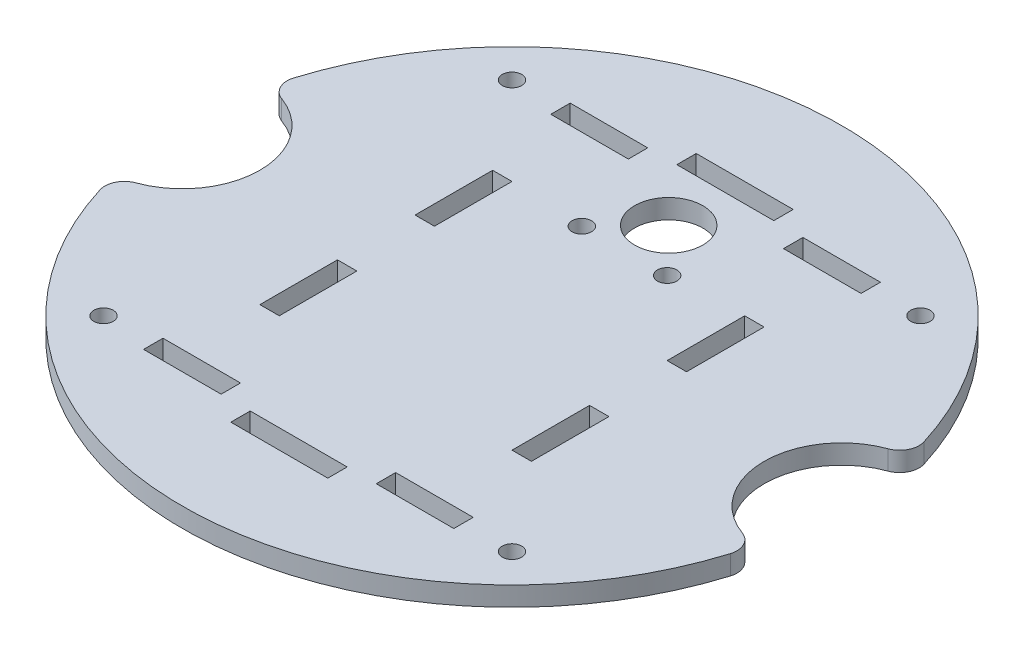
SolidWorks part; units mm, degrees
material "Pine"
ref_plane "Front Plane" through (0, 0, 0) normal (0, 0, 1) x (1, 0, 0)
ref_plane "Top Plane" through (0, 0, 0) normal (0, 1, 0) x (1, 0, 0)
ref_plane "Right Plane" through (0, 0, 0) normal (1, 0, 0) x (0, 0, -1)
sketch "Sketch1" plane through (0, 0, 0) normal (0, 1, 0) x (1, 0, 0)
  line L0 (0, 0) -> (0, 123.9148) construction
  line L1 (0, 0) -> (144.4711, 0) construction
  line L2 (-50.8, 63.5) -> (-25.4, 63.5)
  line L3 (-50.8, 63.5) -> (-50.8, 69.85)
  line L4 (-50.8, 69.85) -> (-25.4, 69.85)
  line L5 (-25.4, 63.5) -> (-25.4, 69.85)
  line L6 (25.4, 63.5) -> (25.4, 69.85)
  line L7 (50.8, 69.85) -> (25.4, 69.85)
  line L8 (50.8, 63.5) -> (50.8, 69.85)
  line L9 (50.8, 63.5) -> (25.4, 63.5)
  line L10 (-25.4, -63.5) -> (-25.4, -69.85)
  line L11 (-50.8, -63.5) -> (-25.4, -63.5)
  line L12 (-50.8, -63.5) -> (-50.8, -69.85)
  line L13 (-50.8, -69.85) -> (-25.4, -69.85)
  line L14 (50.8, -63.5) -> (50.8, -69.85)
  line L15 (50.8, -69.85) -> (25.4, -69.85)
  line L16 (25.4, -63.5) -> (25.4, -69.85)
  line L17 (50.8, -63.5) -> (25.4, -63.5)
  line L18 (38.1, -38.1) -> (44.45, -38.1)
  line L19 (38.1, 38.1) -> (44.45, 38.1)
  line L20 (38.1, 38.1) -> (38.1, 12.7)
  line L21 (38.1, 12.7) -> (44.45, 12.7)
  line L22 (44.45, 38.1) -> (44.45, 12.7)
  line L23 (38.1, -38.1) -> (38.1, -12.7)
  line L24 (38.1, -12.7) -> (44.45, -12.7)
  line L25 (44.45, -38.1) -> (44.45, -12.7)
  line L26 (-38.1, -38.1) -> (-44.45, -38.1)
  line L27 (-44.45, -38.1) -> (-44.45, -12.7)
  line L28 (-38.1, -38.1) -> (-38.1, -12.7)
  line L29 (-38.1, -12.7) -> (-44.45, -12.7)
  line L30 (-38.1, 12.7) -> (-44.45, 12.7)
  line L31 (-38.1, 38.1) -> (-38.1, 12.7)
  line L32 (-38.1, 38.1) -> (-44.45, 38.1)
  line L33 (-44.45, 38.1) -> (-44.45, 12.7)
  line L34 (-15.875, 69.85) -> (-15.875, 76.2)
  line L35 (15.875, -69.85) -> (-15.875, -69.85)
  line L36 (15.875, -69.85) -> (15.875, -76.2)
  line L37 (15.875, -76.2) -> (-15.875, -76.2)
  line L38 (-15.875, -69.85) -> (-15.875, -76.2)
  line L39 (15.875, -69.85) -> (-15.875, -76.2) construction
  line L40 (15.875, -76.2) -> (-15.875, -69.85) construction
  line L41 (15.875, 76.2) -> (-15.875, 76.2)
  line L42 (15.875, 69.85) -> (15.875, 76.2)
  line L43 (15.875, 69.85) -> (-15.875, 69.85)
  arc A0 (-103.1875, -31.7103) -> (103.1875, -31.7103) centre (0, 0) ccw
  circle A1 centre (0, 51.308) radius 11.176
  arc A2 (-99.2841, -23.876) -> (-99.2841, 23.876) centre (-107.95, 0) ccw
  arc A3 (-99.2841, 23.876) -> (-103.1875, 31.7103) centre (-97.1176, 29.845) cw
  arc A4 (-99.2841, -23.876) -> (-103.1875, -31.7103) centre (-97.1176, -29.845) ccw
  arc A5 (99.2841, -23.876) -> (103.1875, -31.7103) centre (97.1176, -29.845) cw
  arc A6 (99.2841, -23.876) -> (99.2841, 23.876) centre (107.95, 0) cw
  arc A7 (99.2841, 23.876) -> (103.1875, 31.7103) centre (97.1176, 29.845) ccw
  arc A8 (103.1875, 31.7103) -> (-103.1875, 31.7103) centre (0, 0) ccw
  arc A9 (-25.2497, 52.1741) -> (-25.0774, 50.6465) centre (3.2211, 54.6124) ccw construction
  arc A11 (4.4749, 49.3063) -> (5.9938, 49.211) centre (5.3694, 51.4101) ccw construction
  circle A12 centre (13.97, 36.83) radius 3.175
  circle A13 centre (-13.97, 36.83) radius 3.175
  circle A14 centre (13.97, 36.83) radius 3.175 construction
  point P52 (0, -73.025)
  point P61 (-25.1738, 51.4092)
  point P66 (5.2262, 49.1286)
  dimension "D1" = 215.9
  dimension "D10" = 22.352
  dimension "D12" = 50.8
  dimension "D13" = 6.35
  dimension "D14" = 6.35
  dimension "D11" = 51.308
  dimension "D2" = 25.4
  dimension "D3" = 25.4
  dimension "D4" = 6.35
  dimension "D5" = 63.5
  dimension "D6" = 6.35
  dimension "D7" = 25.4
  dimension "D8" = 12.7
  dimension "D9" = 38.1
  dimension "D15" = 31.75
  dimension "D16" = 6.35
extrude "Boss-Extrude1" add sketch "Sketch1" along normal blind 6.35
sketch "Sketch2" plane through (0, 0, 0) normal (0, -1, 0) x (1, 0, 0)
  line L0 (0, 0) -> (0, 99.3828) construction
  line L1 (0, 0) -> (-150.0844, 0) construction
  circle A0 centre (-66.8782, 66.8782) radius 3.175
  circle A1 centre (66.8782, 66.8782) radius 3.175
  circle A2 centre (66.8782, -66.8782) radius 3.175
  circle A3 centre (-66.8782, -66.8782) radius 3.175
  dimension "D1" = 6.35
extrude "Cut-Extrude1" cut sketch "Sketch2" against normal up to surface (6.35 mm away) up to face at (0, 6.35, 73.025)
